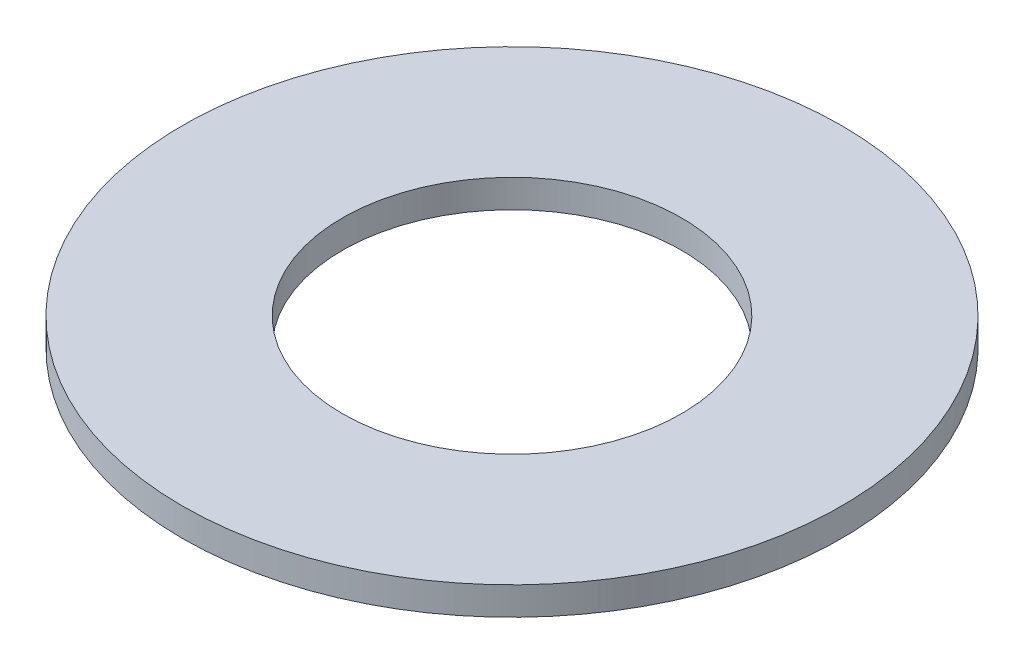
SolidWorks part; units mm, degrees
material "Brass"
ref_plane "Front Plane" through (0, 0, 0) normal (0, 0, 1) x (1, 0, 0)
ref_plane "Top Plane" through (0, 0, 0) normal (0, 1, 0) x (1, 0, 0)
ref_plane "Right Plane" through (0, 0, 0) normal (1, 0, 0) x (0, 0, -1)
sketch "Sketch1" plane through (0, 0, 0) normal (0, 1, 0) x (1, 0, 0)
  circle A0 centre (0, 0) radius 4.7625
  circle A1 centre (0, 0) radius 2.4511
  dimension "D1" = 4.9022
  dimension "D2" = 9.525
extrude "Boss-Extrude1" add sketch "Sketch1" along normal blind 0.4064
